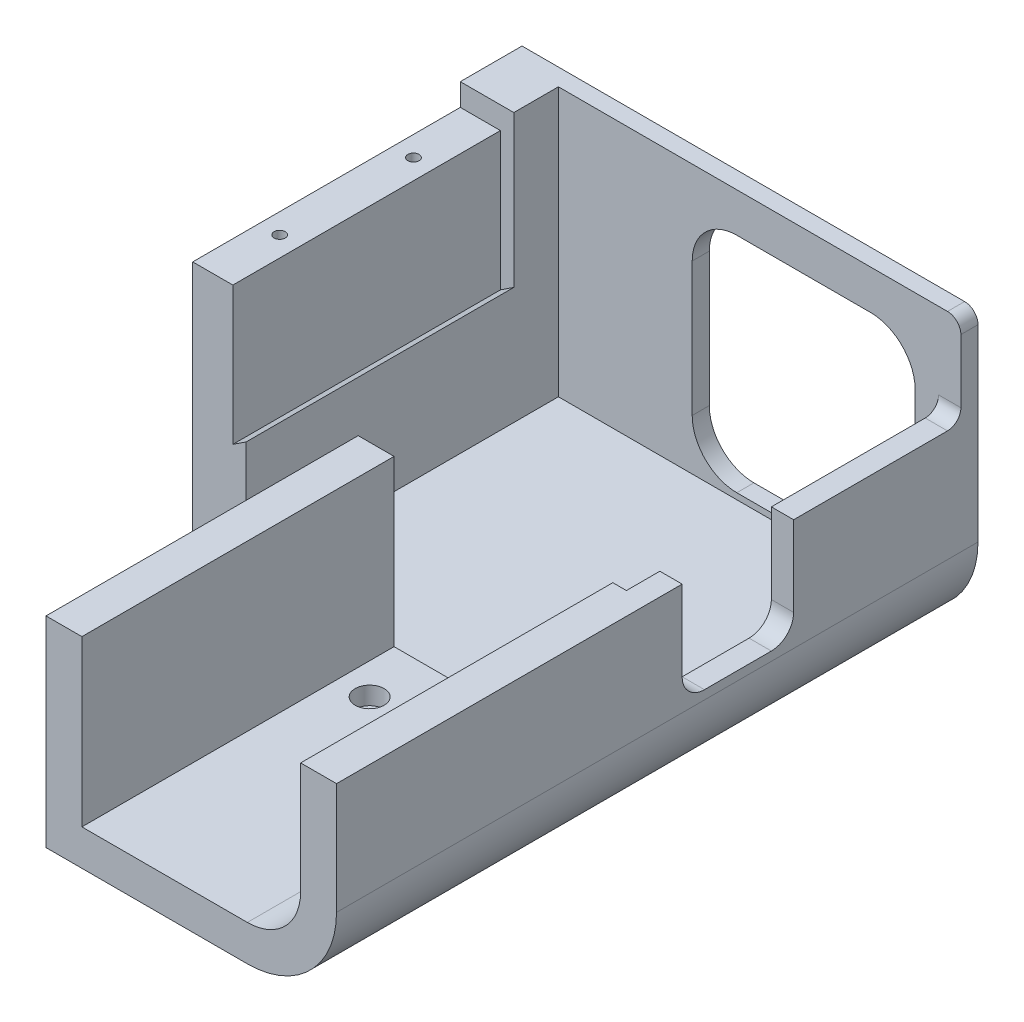
SolidWorks part; units mm, degrees
material "6061 Alloy"
ref_plane "Front Plane" through (0, 0, 0) normal (0, 0, 1) x (1, 0, 0)
ref_plane "Top Plane" through (0, 0, 0) normal (0, 1, 0) x (1, 0, 0)
ref_plane "Right Plane" through (0, 0, 0) normal (1, 0, 0) x (0, 0, -1)
sketch "Sketch2" plane through (0, 0, 0) normal (0, 0, 1) x (1, 0, 0)
  line L0 (85.25, 15) -> (85.25, 45.2)
  line L1 (70.25, 60.2) -> (0, 60.2)
  line L2 (0, 60.2) -> (0, 33.96)
  line L3 (0, 33.96) -> (-3, 35.94)
  line L4 (-3, 35.94) -> (-3, 24.26)
  line L6 (-3, 24.26) -> (0, 26.24)
  line L7 (0, 26.24) -> (0, 0)
  line L8 (0, 0) -> (70.25, 0)
  line L9 (30, 41.37) -> (30, 11.37)
  line L10 (40, 1.37) -> (70, 1.37)
  line L11 (80, 11.37) -> (80, 41.37)
  line L12 (70, 51.37) -> (40, 51.37)
  arc A0 (70.25, 0) -> (85.25, 15) centre (70.25, 15) ccw
  arc A1 (85.25, 45.2) -> (70.25, 60.2) centre (70.25, 45.2) ccw
  arc A2 (30, 11.37) -> (40, 1.37) centre (40, 11.37) ccw
  arc A3 (70, 1.37) -> (80, 11.37) centre (70, 11.37) ccw
  arc A4 (80, 41.37) -> (70, 51.37) centre (70, 41.37) ccw
  arc A5 (40, 51.37) -> (30, 41.37) centre (40, 41.37) ccw
  dimension "D3" = 15
  dimension "D4" = 3
  dimension "D7" = 10
  dimension "D1" = 85.25
  dimension "D2" = 60.2
  dimension "D5" = 11.68
  dimension "D6" = 7.72
  dimension "D8" = 50
  dimension "D9" = 50
  dimension "D10" = 5.25
  dimension "D11" = 1.37
ref_plane "Plane1" through (0, 0, 70) normal (0, 0, 1) x (1, 0, 0)
sketch "Sketch4" plane through (0, 0, 70) normal (0, 0, 1) x (1, 0, 0)
  line L0 (82.2, 15) -> (82.2, 45.2)
  line L1 (70.25, 57.15) -> (33.15, 57.15)
  line L2 (33.15, 57.15) -> (33.15, 3.05)
  line L3 (33.15, 3.05) -> (70.25, 3.05)
  line L4 (85.25, 15) -> (85.25, 45.2) construction
  line L5 (0, 0) -> (70.25, 0) construction
  arc A0 (82.2, 45.2) -> (70.25, 57.15) centre (70.25, 45.2) ccw
  arc A1 (70.25, 3.05) -> (82.2, 15) centre (70.25, 15) ccw
  dimension "D3" = 11.95
  dimension "D1" = 54.1
  dimension "D2" = 49.05
  dimension "D4" = 3.05
  dimension "D5" = 3.05
sketch "Sketch3" plane through (0, 0, 0) normal (0, 0, 1) x (1, 0, 0)
  line L0 (85.25, 15) -> (85.25, 45.2) construction
  line L1 (0, 0) -> (70.25, 0) construction
  line L2 (0, 26.24) -> (0, 0) construction
  line L5 (85.25, 15) -> (85.25, 40)
  line L6 (0, 0) -> (70.25, 0)
  line L7 (0, 60.2) -> (0, 0)
  line L10 (0, 60.2) -> (-12, 60.2)
  line L11 (-12, -5) -> (70.25, -5)
  line L12 (90.25, 15) -> (90.25, 40)
  line L13 (0, -5) -> (70.25, -5) construction
  line L14 (-12, 60.2) -> (-12, -5)
  line L15 (85.25, 40) -> (90.25, 40)
  arc A0 (70.25, 0) -> (85.25, 15) centre (70.25, 15) ccw construction
  arc A1 (70.25, 0) -> (85.25, 15) centre (70.25, 15) ccw
  arc A2 (70.25, -5) -> (90.25, 15) centre (70.25, 15) ccw
  dimension "D1" = 5
  dimension "D2" = 40
  dimension "D3" = 12
extrude "Boss-Extrude1" add sketch "Sketch3" along normal up to surface (70 mm away) up to plane "Plane1"
sketch "Sketch5" plane through (0, 0, 70) normal (0, 0, 1) x (1, 0, 0)
  line L0 (82.2, 15) -> (82.2, 45.2) construction
  line L1 (33.15, 3.05) -> (70.25, 3.05) construction
  line L2 (33.15, 57.15) -> (33.15, 3.05) construction
  line L3 (82.2, 15) -> (82.2, 40)
  line L4 (33.15, 3.05) -> (70.25, 3.05)
  line L5 (33.15, 40) -> (33.15, 3.05)
  line L6 (25.1, 40) -> (25.1, -5)
  line L7 (25.1, -5) -> (70.25, -5)
  line L8 (90.25, 15) -> (90.25, 40)
  line L9 (33.15, 57.15) -> (33.15, 3.05) construction
  line L10 (25.1, 57.15) -> (25.1, -5) construction
  line L11 (25.1, 40) -> (33.15, 40)
  line L12 (82.2, 40) -> (90.25, 40)
  arc A0 (70.25, 3.05) -> (82.2, 15) centre (70.25, 15) ccw construction
  arc A1 (70.25, 3.05) -> (82.2, 15) centre (70.25, 15) ccw
  arc A2 (70.25, -5) -> (90.25, 15) centre (70.25, 15) ccw
  dimension "D1" = 8.05
extrude "Boss-Extrude2" add sketch "Sketch5" along normal blind 70
sketch "Sketch6" plane through (0, 0, 70) normal (0, 0, 1) x (1, 0, 0)
  line L0 (-3, 24.26) -> (0, 26.24) construction
  line L1 (-3, 35.94) -> (-3, 24.26) construction
  line L2 (-3, 24.26) -> (0, 26.24)
  line L3 (-3, 60.2) -> (-3, 24.26)
  line L4 (0, 60.2) -> (-12, 60.2) construction
  line L5 (0, 26.24) -> (0, 60.2)
  line L6 (0, 60.2) -> (-3, 60.2)
extrude "Cut-Extrude1" cut sketch "Sketch6" against normal offset from surface (60 mm away) 10 up to face at (47.4749, 21.3151, 0)
sketch "Sketch13" plane through (0, 60.2, 0) normal (0, 1, 0) x (1, 0, 0)
  line L0 (-35.86, -70) -> (35.86, -70) construction
  line L1 (-3, -10) -> (-12, -10)
  line L2 (-3, -10) -> (-3, -70)
  line L3 (-3, -70) -> (-12, -70)
  line L4 (-12, -10) -> (-12, -70)
  line L5 (-12, -70) -> (-12, 0) construction
extrude "Cut-Extrude3" cut sketch "Sketch13" against normal blind 5
sketch "Sketch12" plane through (90.25, 0, 0) normal (1, 0, 0) x (0, 0, -1)
  line L0 (-70, 35.86) -> (-70, -35.86) construction
  line L2 (-62.5, 17) -> (-37.5, 17)
  line L3 (-62.5, 17) -> (-62.5, 40)
  line L4 (-62.5, 40) -> (-37.5, 40)
  line L5 (-37.5, 17) -> (-37.5, 40)
  line L9 (0, 15) -> (0, 45.2) construction
  line L10 (-140, 40) -> (0, 40) construction
  circle A0 centre (-50, 30.1) radius 7.5 construction
  point P13 (0, 30.1)
  point P17 (-50, 40)
  dimension "D1" = 15
  dimension "D2" = 20
  dimension "D3" = 25
  dimension "D4" = 23
extrude "Cut-Extrude2" cut sketch "Sketch12" against normal up to surface (5 mm away) up to face at (85.25, 27.5, 35)
sketch "Sketch7" plane through (0, 0, 0) normal (0, 0, 1) x (1, 0, 0)
  line L0 (70, 51.37) -> (40, 51.37) construction
  line L1 (30, 41.37) -> (30, 11.37) construction
  line L2 (40, 1.37) -> (70, 1.37) construction
  line L3 (80, 11.37) -> (80, 41.37) construction
  line L4 (70, 51.37) -> (40, 51.37)
  line L5 (30, 41.37) -> (30, 11.37)
  line L6 (40, 1.37) -> (70, 1.37)
  line L7 (80, 11.37) -> (80, 41.37)
  line L8 (-12, 60.2) -> (-12, -5) construction
  line L9 (-12, -5) -> (70.25, -5) construction
  line L10 (90.25, 15) -> (90.25, 40) construction
  line L11 (-12, 60.2) -> (-12, -5)
  line L12 (-12, -5) -> (70.25, -5)
  line L13 (90.25, 15) -> (90.25, 60.2)
  line L14 (0, 60.2) -> (-12, 60.2) construction
  line L15 (90.25, 60.2) -> (-12, 60.2)
  arc A0 (80, 41.37) -> (70, 51.37) centre (70, 41.37) ccw construction
  arc A1 (40, 51.37) -> (30, 41.37) centre (40, 41.37) ccw construction
  arc A2 (30, 11.37) -> (40, 1.37) centre (40, 11.37) ccw construction
  arc A3 (70, 1.37) -> (80, 11.37) centre (70, 11.37) ccw construction
  arc A4 (80, 41.37) -> (70, 51.37) centre (70, 41.37) ccw
  arc A5 (40, 51.37) -> (30, 41.37) centre (40, 41.37) ccw
  arc A6 (30, 11.37) -> (40, 1.37) centre (40, 11.37) ccw
  arc A7 (70, 1.37) -> (80, 11.37) centre (70, 11.37) ccw
  arc A8 (70.25, -5) -> (90.25, 15) centre (70.25, 15) ccw construction
  arc A9 (70.25, -5) -> (90.25, 15) centre (70.25, 15) ccw
extrude "Boss-Extrude3" add sketch "Sketch7" against normal blind 3.84
hole_wizard "CBORE for M3 SHCS1" positions "Sketch10" profile "Sketch11" counterbore size "M3" standard "ANSI Metric"
sketch "Sketch10" plane through (0, 3.05, 0) normal (0, 1, 0) x (1, 0, 0)
  line L1 (25.1, -70) -> (70.25, -70) construction
  line L2 (25.1, -70) -> (25.1, -95) construction
  line L3 (25.1, -95) -> (70.25, -95) construction
  line L4 (70.25, -70) -> (70.25, -95) construction
  line L5 (40.175, -82.5) -> (55.175, -82.5) construction
  line L8 (70.25, -140) -> (70.25, -70) construction
  point P0 (40.175, -82.5)
  point P2 (55.175, -82.5)
  point P58 (25.1, -82.5)
  point P59 (47.675, -82.5)
  point P60 (47.675, -95)
  dimension "D1" = 15
  dimension "D2" = 45.15
  dimension "D3" = 25
sketch "Sketch11" plane through (40.175, 3.05, 82.5) normal (1, 0, 0) x (0, 0, 1)
  line L0 (0, 0) -> (0, 9.0715)
  line L1 (0, 9.0715) -> (1.7, 8.05)
  line L2 (1.7, 8.05) -> (1.7, 4)
  line L3 (1.7, 4) -> (3.25, 4)
  line L4 (3.25, 4) -> (3.25, 0)
  line L5 (3.25, 0) -> (0, 0)
  line L10 (0, 9.0715) -> (-1.7, 8.05) construction
  line L11 (0, -6.35) -> (0, 107.95) construction
  dimension "Hole Dia." = 3.4
  dimension "Hole Depth" = 8.05
  dimension "C'Bore Dia." = 6.5
  dimension "C'Bore Depth" = 4
  dimension "Drill Angle" = 118
hole_wizard "M3x0.5 Tapped Hole1" positions "Sketch14" profile "Sketch15" tap size "M3x0.5" standard "ANSI Metric"
sketch "Sketch14" plane through (0, 55.2, 0) normal (0, 1, 0) x (1, 0, 0)
  line L0 (-7.5, -25) -> (-7.5, -55) construction
  line L2 (-12, -10) -> (-12, -70) construction
  line L3 (-3, -10) -> (-12, -10) construction
  point P0 (-7.5, -25)
  point P2 (-7.5, -55)
  point P11 (-12, -40)
  point P12 (-7.5, -40)
  point P15 (-7.5, -10)
  dimension "D1" = 30
sketch "Sketch15" plane through (-7.5, 55.2, 25) normal (1, 0, 0) x (0, 0, 1)
  line L0 (0, 0) -> (0, 14.7511)
  line L1 (0, 14.7511) -> (1.25, 14)
  line L2 (1.25, 14) -> (1.25, 0)
  line L5 (1.25, 0) -> (0, 0)
  line L10 (0, 14.7511) -> (-1.25, 14) construction
  line L11 (0, -6.35) -> (0, 107.95) construction
  dimension "Tap Drill Dia." = 2.5
  dimension "Tap Drill Depth" = 14
  dimension "Drill Angle" = 118
cosmetic thread "Hole Thread1" parameters "D1"=6, "D2"=3
cosmetic thread "Hole Thread2" parameters "D1"=6, "D2"=3
fillet "Fillet1" radius 10 1 edges at (25.1, -2.5, 70)
fillet "Fillet4" radius 5 2 edges at (87.75, 17, 37.5) (87.75, 17, 62.5)
fillet "Fillet5" radius 3 2 edges at (87.75, 40, 0) (90.25, 60.2, -1.92)
